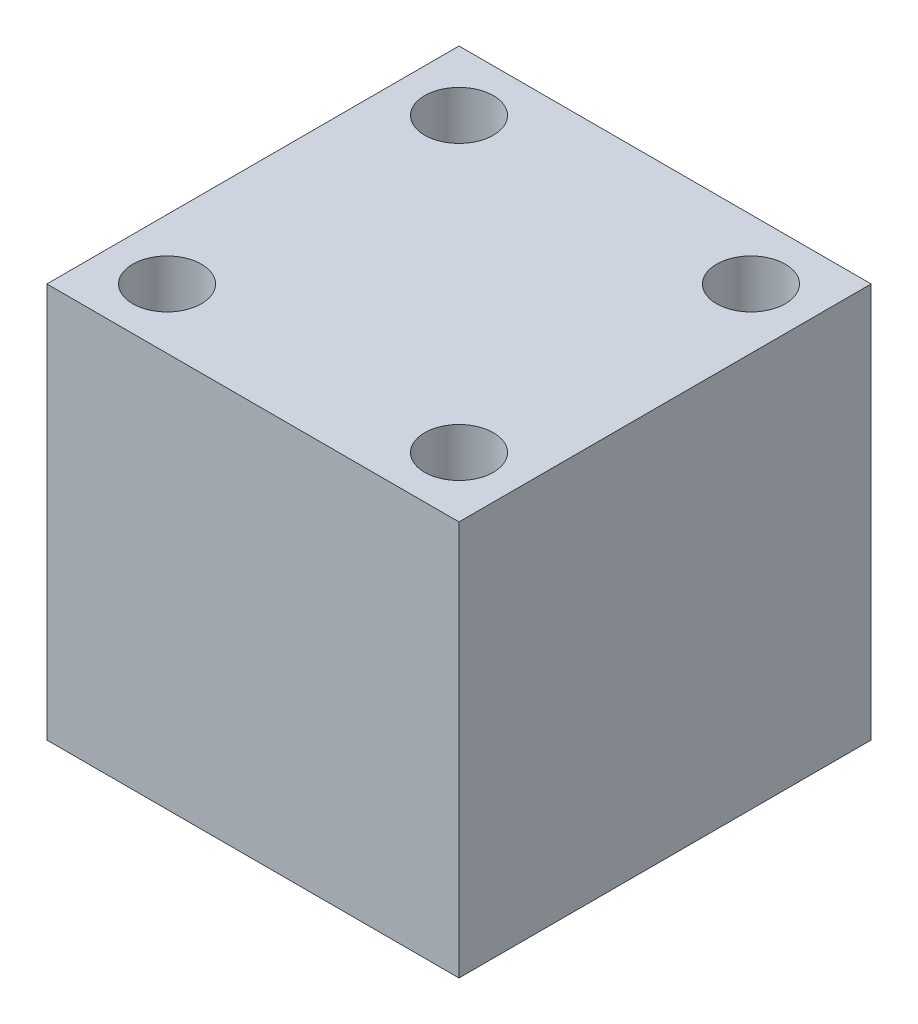
SolidWorks part; units mm, degrees
other "ﾏｰｸｱｯﾌﾟ1"
sketch "ｽｹｯﾁ3" plane through (36, -5.7795, 6.7) normal (0.542, 0.6669, 0.5113) x (0.638, 0.0695, -0.7669)
ref_plane "正面" through (0, 0, 0) normal (0, 0, 1) x (1, 0, 0)
ref_plane "平面" through (0, 0, 0) normal (0, 1, 0) x (1, 0, 0)
ref_plane "右側面" through (0, 0, 0) normal (1, 0, 0) x (0, 0, -1)
sketch "ｽｹｯﾁ1" plane through (0, 0, 0) normal (0, 0, 1) x (1, 0, 0)
  line L1 (0, -5.7795) -> (36, -5.7795)
  line L2 (0, -5.7795) -> (0, -40.2795)
  line L3 (0, -40.2795) -> (36, -40.2795)
  line L4 (36, -5.7795) -> (36, -40.2795)
  dimension "D1" = 34.5
  dimension "D2" = 36
extrude "ﾎﾞｽ - 押し出し1" add sketch "ｽｹｯﾁ1" along normal blind 36 from surface
sketch "ｽｹｯﾁ2" plane through (0, -5.7795, 0) normal (0, 1, 0) x (1, 0, 0)
  line L0 (36, -7) -> (36, 29) construction
  line L1 (30.75, 23.75) -> (5.25, 23.75) construction
  line L2 (30.75, 23.75) -> (30.75, -1.75) construction
  line L3 (30.75, -1.75) -> (5.25, -1.75) construction
  line L4 (5.25, 23.75) -> (5.25, -1.75) construction
  line L5 (0, 29) -> (36, 29) construction
  circle A0 centre (30.75, 23.75) radius 3
  circle A1 centre (30.75, -1.75) radius 3
  circle A2 centre (5.25, -1.75) radius 3
  circle A3 centre (5.25, 23.75) radius 3
  point P10 (36, 11)
  point P11 (30.75, 11)
  point P14 (18, 29)
  point P15 (18, 23.75)
  dimension "D1" = 6
  dimension "D2" = 25.5
  dimension "D3" = 25.5
extrude "ｶｯﾄ - 押し出し1" cut sketch "ｽｹｯﾁ2" against normal blind 5
